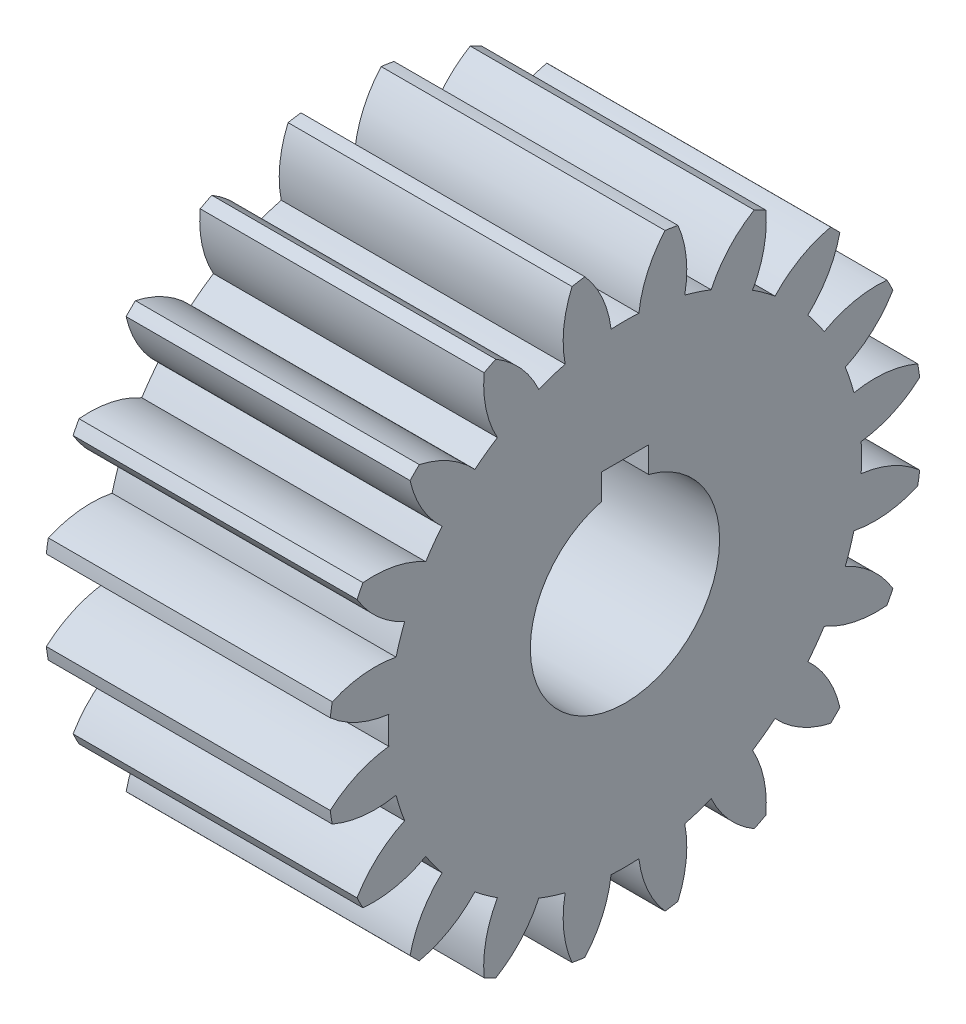
SolidWorks part; units mm, degrees
material "Alumina"
ref_plane "Plane1" through (0, 0, 0) normal (0, 0, 1) x (1, 0, 0)
ref_plane "Plane2" through (0, 0, 0) normal (0, 1, 0) x (1, 0, 0)
ref_plane "Plane3" through (0, 0, 0) normal (1, 0, 0) x (0, 0, -1)
sketch "HoldingSke" plane through (0, 0, 0) normal (0, 1, 0) x (1, 0, 0)
  line L0 (0, 0) -> (334.1547, -121.6224)
  line L1 (-15, 0) -> (100, 0) construction
  line L2 (0, 0) -> (-2.1039, 2.3779)
  line L3 (0, 0) -> (-11.863, 4.5341)
  line L4 (0, 0) -> (8.1152, 2.9537)
  line L5 (0, 0) -> (-47.5972, -17.7524)
  line L6 (0, 0) -> (-15.7917, -10.6547)
  line L7 (-2.1039, 2.3779) -> (8.8308, 51.9871)
  line L8 (-76.2, 54.61) -> (-62.3824, 54.61)
  line L9 (-71.009, 38.7566) -> (-53.1078, 45.2721)
  line L10 (-76.2, 71.12) -> (104.1128, 71.12)
  line L11 (0, 0) -> (-19.05, 0)
  line L12 (-76.2, 101.6) -> (-76.1147, 101.6)
  line L13 (24.9733, 27.94) -> (52.9518, 28.4284)
  line L14 (24.9733, 27.94) -> (24.9746, 27.94)
  line L15 (24.9733, 27.94) -> (100.4006, 29.5858)
  circle A0 centre (0, 0) radius 6.35
  circle A1 centre (0, 0) radius 15.8737
  circle A2 centre (0, 0) radius 38.1
  circle A3 centre (0, 0) radius 6.35
  dimension "MHD" = 31.7475
  dimension "Hub_dia" = 76.2
  dimension "Bore" = 12.7
  dimension "MBD" = 12.7
  dimension "Num_teeth" = 20
  dimension "Pitch" = 355.6
  dimension "Overall_len" = 50.8
  dimension "Show_teeth" = 20
  dimension "Thickness" = 19.05
  dimension "OAL" = 50.8001
  dimension "T_dim" = 13.8176
  dimension "Ap" = 20
  dimension "H" = 19.05
  dimension "Pitch_radius" = 180.3128
  dimension "Width" = 19.05
  dimension "Backlash" = 0.0853
  dimension "Addendum_fac" = 1
  dimension "Dedendum_fac" = 1.25
  dimension "Clearance_fac" = 0.25
  dimension "Dedendum_add" = 0.0013
sketch "BasProSke" plane through (0, 0, 0) normal (0, 1, 0) x (1, 0, 0)
  line L0 (-10, 0) -> (60, 0) construction
  line L1 (0, 0) -> (0, 19.9571)
  line L2 (0, 0) -> (19.05, 0)
  line L3 (19.05, 0) -> (19.05, 19.9571)
  line L4 (19.05, 19.9571) -> (0, 19.9571)
  dimension "Thickness" = 19.05
  dimension "Diameter" = 39.9143
revolve "Base-Revolve" add sketch "BasProSke" angle 360 about L0
sketch "TooCutSke" plane through (0, 0, 0) normal (1, 0, 0) x (0, 0, -1)
  line L1 (0, 0) -> (0, 107) construction
  line L2 (0, 0) -> (-1.5727, 18.0746) construction
  line L3 (0, 0) -> (-5.6623, 35.7505) construction
  line L4 (-1.5727, 18.0746) -> (-2.8312, 17.8752) construction
  arc A0 (0.9322, 15.8463) -> (-0.9322, 15.8463) centre (0, 0) ccw
  arc A1 (2.7094, 19.798) -> (-2.7094, 19.798) centre (0, 0) ccw
  circle A2 centre (0, 0) radius 18.1429 construction
  circle A3 centre (0, 0) radius 17.0487 construction
  arc A4 (-0.9322, 15.8463) -> (-2.7094, 19.798) centre (-8.1376, 14.9813) ccw
  arc A5 (2.7094, 19.798) -> (0.9322, 15.8463) centre (8.1376, 14.9813) ccw
  dimension "Root_dia" = 31.7475
  dimension "Overcut_dia" = 39.9651
  dimension "Pitch_dia" = 36.2857
  dimension "Base_dia" = 34.0974
  dimension "Flank_rad" = 7.2571
  dimension "Half_ang" = 9
  dimension "Half_CT" = 1.2741
extrude "ToothCut" cut sketch "TooCutSke" along normal through all
fillet "Breaks" [suppressed] radius 0.0363
fillet "RootFillets" [suppressed] radius 0.4548
pattern_circular "TeethCuts" count 20 over 360 about axis through (0, 0, 0) along (1, 0, 0) of "ToothCut", "RootFillets", "Breaks"
sketch "HubNeaOneSke" plane through (0, 0, 0) normal (-1, 0, 0) x (0, 0, 1)
  circle A0 centre (0, 0) radius 15.8737
  dimension "Diameter" = 31.7475
extrude "HubNearOne" [suppressed] add sketch "HubNeaOneSke" along normal blind 31.7501
sketch "HubNeaBotSke" plane through (0, 0, 0) normal (-1, 0, 0) x (0, 0, 1)
  circle A0 centre (0, 0) radius 15.8737
  dimension "Diameter" = 31.7475
extrude "HubNearBoth" [suppressed] add sketch "HubNeaBotSke" along normal blind 15.875
ref_plane "FarPln" through (19.05, 0, 0) normal (1, 0, 0) x (0, 0, -1)
sketch "HubFarSke" plane through (19.05, 0, 0) normal (1, 0, 0) x (0, 0, -1)
  circle A0 centre (0, 0) radius 15.8737
  dimension "Diameter" = 31.7475
extrude "HubFar" [suppressed] add sketch "HubFarSke" along normal blind 15.875
sketch "BorSke" plane through (0, 0, 0) normal (1, 0, 0) x (0, 0, -1)
  circle A0 centre (0, 0) radius 6.35
  dimension "Diameter" = 12.7
extrude "Bore" cut sketch "BorSke" along normal mid plane 101.6001
sketch "KeySke" plane through (0, 0, 0) normal (1, 0, 0) x (0, 0, -1)
  line L0 (-1.5875, 0) -> (-1.5875, 7.4676)
  line L1 (-1.5875, 7.4676) -> (1.5875, 7.4676)
  line L2 (1.5875, 7.4676) -> (1.5875, 0)
  line L3 (0, 0) -> (0, 34) construction
  line L4 (-1.5875, 0) -> (1.5875, 0)
  dimension "Offset" = 7.4676
  dimension "Width" = 3.175
extrude "Keyway" cut sketch "KeySke" along normal mid plane 101.6001
pattern_circular "Keyway2" [suppressed] count 2 every 90 about axis through (-10, 0, 0) along (1, 0, 0)
sketch "Sketch1" plane through (19.05, 0, 0) normal (1, 0, 0) x (0, 0, -1)
  line L1 (-1.5875, 7.4676) -> (-1.5875, 7.874)
  line L2 (1.5875, 7.4676) -> (1.5875, 7.874)
  line L3 (-1.5875, 7.874) -> (1.5875, 7.874)
extrude "Cut-Extrude4" cut sketch "Sketch1" against normal through all and the other way through all
equation "' \"Pitch@HoldingSke\" = 4"
equation "' \"Num_teeth@HoldingSke\" = 12"
equation "' \"Ap@HoldingSke\" =  20"
equation "' \"Ap@HoldingSke\" = 20"
equation "' \"Width@HoldingSke\" = 0.5"
equation "' \"Hub_dia@HoldingSke\"= 1"
equation "' \"Hub_dia@HoldingSke\" = 1"
equation "' \"Overall_len@HoldingSke\" = 1.0"
equation "' \"Bore@HoldingSke\" = 0.75"
equation "' \"T_dim@HoldingSke\" = 0.85"
equation "' \"Width@KeySke\" = 0.25"
equation "' \"Show_teeth@HoldingSke\" = 13"
equation "' \"Backlash@HoldingSke\" = 0.009"
equation "' \"Addendum_fac@HoldingSke\" = 1.0"
equation "' \"Dedendum_fac@HoldingSke\" = 1.25"
equation "' \"Dedendum_add@HoldingSke\" = 0.00005"
equation "' \"Clearance_fac@HoldingSke\" = 0.25"
equation "' \"Pitch@HoldingSke\" = 0.5"
equation "' \"Num_teeth@HoldingSke\" = 23"
equation "' \"Show_teeth@HoldingSke\" = 23"
equation "' \"Backlash@HoldingSke\" = 0.0375"
equation "\"Overcut_dia@TooCutSke\" = (\"Num_teeth@HoldingSke\" + 2 * \"Addendum_fac@HoldingSke\") / \"Pitch@HoldingSke\" + 0.002"
equation "\"Pitch_dia@TooCutSke\" = \"Num_teeth@HoldingSke\" / \"Pitch@HoldingSke\""
equation "\"Base_dia@TooCutSke\" = \"Num_teeth@HoldingSke\" / \"Pitch@HoldingSke\" * cos((\"Ap@HoldingSke\"  * 3.14159265 / 180))"
equation "\"Root_dia@TooCutSke\" = (\"Num_teeth@HoldingSke\" + 2) / \"Pitch@HoldingSke\" - 2 * (\"Addendum_fac@HoldingSke\" + \"Dedendum_fac@HoldingSke\") / \"Pitch@HoldingSke\" - \"Dedendum_add@HoldingSke\" * 2"
equation "\"Half_ang@TooCutSke\" = 180 / \"Num_teeth@HoldingSke\""
equation "\"Half_CT@TooCutSke\" = \"Num_teeth@HoldingSke\" / \"Pitch@HoldingSke\" * sin((3.14159265 / 2 / \"Num_teeth@HoldingSke\")) / 2 - 7 * \"Backlash@HoldingSke\" / 4"
equation "\"Flank_rad@TooCutSke\" = \"Num_teeth@HoldingSke\" / \"Pitch@HoldingSke\" / 5"
equation "\"Radius@RootFillets\" = \"Clearance_fac@HoldingSke\" / \"Pitch@HoldingSke\" + \"Dedendum_add@HoldingSke\""
equation "\"Break_rad@Breaks\" = 0.02 / \"Pitch@HoldingSke\""
equation "\"Thickness@HoldingSke\" = \"Width@HoldingSke\""
equation "\"OAL@HoldingSke\" = \"Thickness@HoldingSke\""
equation "\"MHD@HoldingSke\" = (\"Num_teeth@HoldingSke\" + 2) / \"Pitch@HoldingSke\" - 2 * (\"Addendum_fac@HoldingSke\" + \"Dedendum_fac@HoldingSke\")  / \"Pitch@HoldingSke\" - \"Dedendum_add@HoldingSke\" * 2"
equation "\"MBD@HoldingSke\" = (\"Num_teeth@HoldingSke\" + 2) / \"Pitch@HoldingSke\" - 2 * (\"Addendum_fac@HoldingSke\" + \"Dedendum_fac@HoldingSke\")  / \"Pitch@HoldingSke\" - \"Dedendum_add@HoldingSke\" * 2 - 0.002"
equation "\"MHD@HoldingSke\" = ((sgn( \"MHD@HoldingSke\" - \"Hub_dia@HoldingSke\" )-1)*( \"MHD@HoldingSke\" - \"Hub_dia@HoldingSke\" ))/-2+ \"Hub_dia@HoldingSke\""
equation "\"MBD@HoldingSke\" = ((sgn( \"MBD@HoldingSke\" - \"Bore@HoldingSke\" )-1)*( \"MBD@HoldingSke\" - \"Bore@HoldingSke\" ))/-2+ \"Bore@HoldingSke\""
equation "\"OAL@HoldingSke\" = ((sgn( \"OAL@HoldingSke\" - \"Overall_len@HoldingSke\" )+1)*( \"OAL@HoldingSke\" - \"Overall_len@HoldingSke\" ))/2 + \"Overall_len@HoldingSke\" + 0.000002"
equation "\"Num_teeth@TeethCuts\" = int( \"Show_teeth@HoldingSke\" ) + 1"
equation "\"Num_teeth@TeethCuts\" = ((sgn( \"Num_teeth@TeethCuts\" - \"Num_teeth@HoldingSke\" )-1)*( \"Num_teeth@TeethCuts\" - \"Num_teeth@HoldingSke\" ))/-2+ \"Num_teeth@HoldingSke\""
equation "\"Num_teeth@TeethCuts\" = ((sgn( \"Num_teeth@TeethCuts\" - 2.0)+1)*( \"Num_teeth@TeethCuts\" - 2.0))/2 +2.0"
equation "\"Angle@TeethCuts\" = 360.0 / \"Num_teeth@HoldingSke\""
equation "\"Diameter@BasProSke\" = (\"Num_teeth@HoldingSke\" + 2 * \"Addendum_fac@HoldingSke\") / \"Pitch@HoldingSke\""
equation "\"Thickness@BasProSke\"  = \"Thickness@HoldingSke\""
equation "' \"Fillet_rad@BasProSke\" =  \"Thickness@HoldingSke\" * 0.05"
equation "' \"Fillet_rad@BasProSke\" = \"Thickness@HoldingSke\" * 0.05"
equation "\"MHD@HoldingSke\" = ((sgn( \"MHD@HoldingSke\" - \"Root_dia@TooCutSke\" )-1)*( \"MHD@HoldingSke\" - \"Root_dia@TooCutSke\" ))/-2+ \"Root_dia@TooCutSke\""
equation "\"Diameter@HubNeaOneSke\" = \"MHD@HoldingSke\""
equation "\"Length@HubNearOne\" = \"OAL@HoldingSke\" - \"Thickness@BasProSke\""
equation "\"Diameter@HubNeaBotSke\" = \"MHD@HoldingSke\""
equation "\"Length@HubNearBoth\" = ( \"OAL@HoldingSke\" - \"Thickness@BasProSke\" ) / 2.0"
equation "\"Thickness@FarPln\" = \"Thickness@BasProSke\""
equation "\"Diameter@HubFarSke\" = \"MHD@HoldingSke\""
equation "\"Length@HubFar\" = ( \"OAL@HoldingSke\" - \"Thickness@BasProSke\" ) / 2.0"
equation "\"Diameter@BorSke\" = \"MBD@HoldingSke\""
equation "\"D1@Bore\" = \"OAL@HoldingSke\" * 2.0"
equation "\"D1@Keyway\" = \"OAL@HoldingSke\" * 2.0"
equation "\"Offset@KeySke\" = \"T_dim@HoldingSke\" - \"MBD@HoldingSke\" / 2.0"
